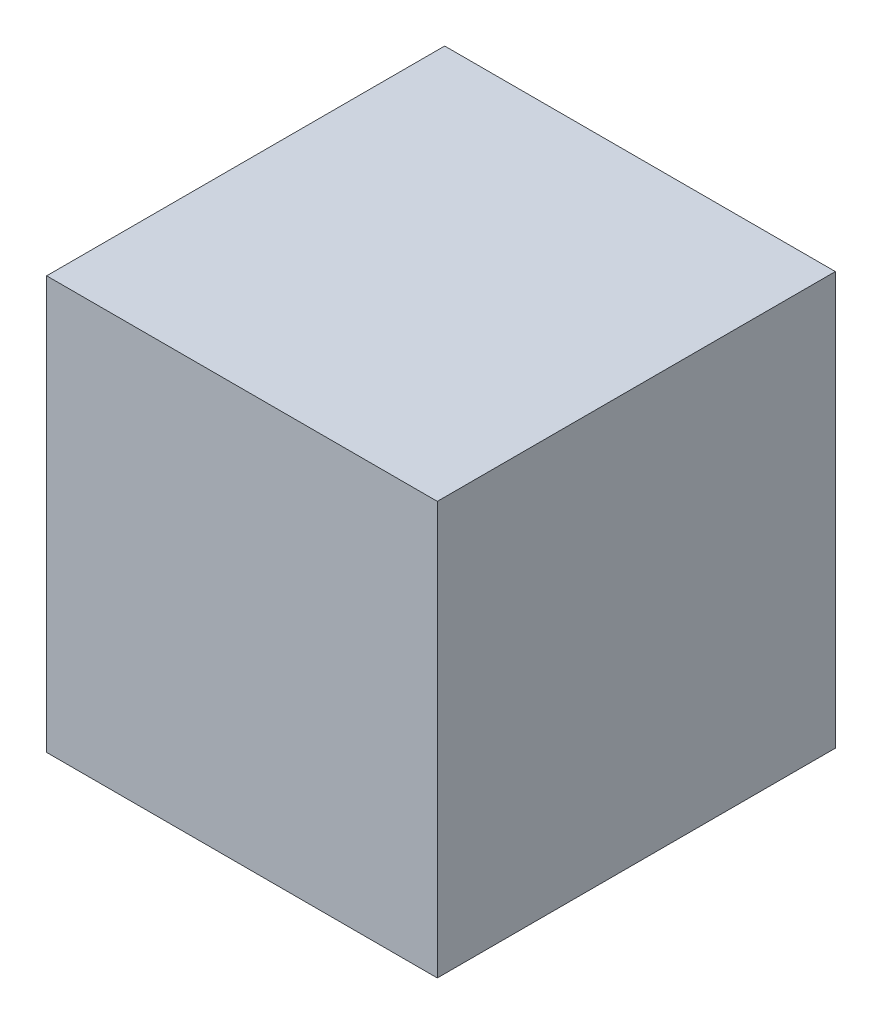
SolidWorks part; units mm, degrees
ref_plane "Front Plane" through (0, 0, 0) normal (0, 0, 1) x (1, 0, 0)
ref_plane "Top Plane" through (0, 0, 0) normal (0, 1, 0) x (1, 0, 0)
ref_plane "Right Plane" through (0, 0, 0) normal (1, 0, 0) x (0, 0, -1)
sketch "Sketch1" plane through (0, 0, 0) normal (0, 0, 1) x (1, 0, 0)
  line L1 (0, 0) -> (168.275, 0)
  line L2 (0, 0) -> (0, 177.8)
  line L3 (0, 177.8) -> (168.275, 177.8)
  line L4 (168.275, 0) -> (168.275, 177.8)
  dimension "D1" = 168.275
  dimension "D2" = 177.8
extrude "Boss-Extrude1" add sketch "Sketch1" along normal blind 171.45
